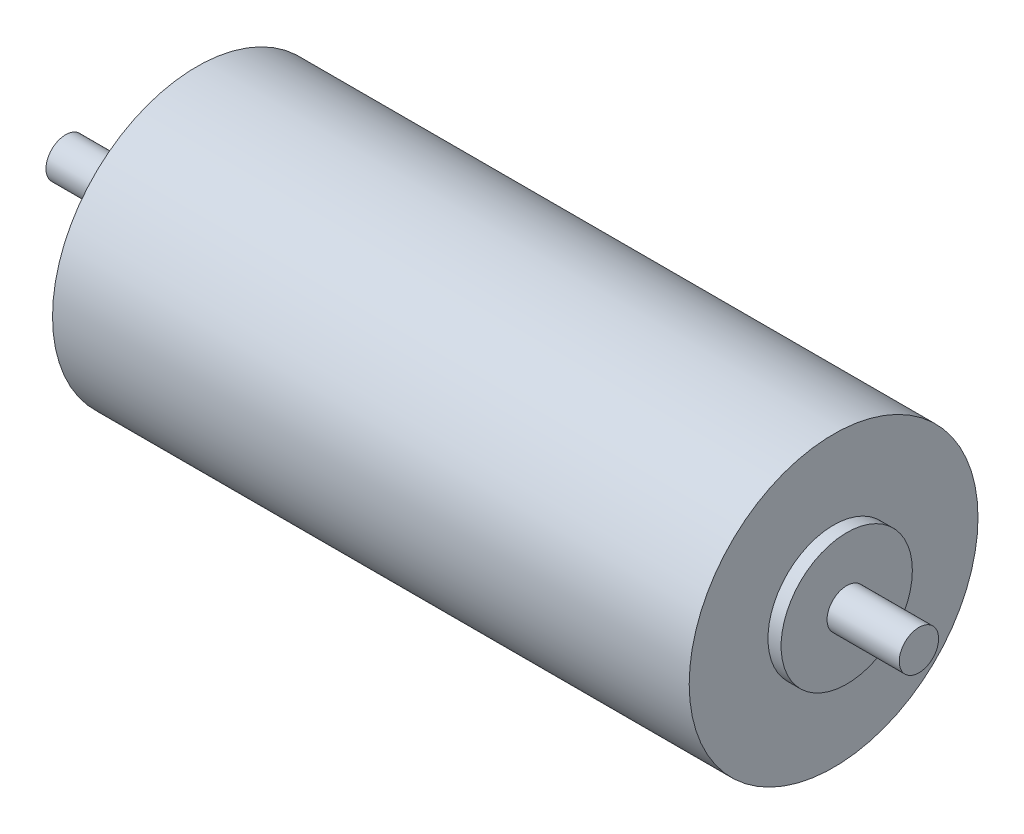
SolidWorks part; units mm, degrees
ref_plane "Vorne" through (0, 0, 0) normal (0, 0, 1) x (1, 0, 0)
ref_plane "Oben" through (0, 0, 0) normal (0, 1, 0) x (1, 0, 0)
ref_plane "Rechts" through (0, 0, 0) normal (1, 0, 0) x (0, 0, -1)
ref_plane "Ebene1" through (0, -15, 0) normal (0, 1, 0) x (1, 0, 0)
sketch "Skizze2" plane through (0, 0, 0) normal (0, 0, 1) x (1, 0, 0)
  line L0 (56.6731, 0) -> (-12.9638, 0) construction
  line L1 (-10, 0) -> (-10, 1.5)
  line L4 (-10, 1.5) -> (-1, 1.5)
  line L6 (-1, 1.5) -> (-1, 5)
  line L7 (-1, 5) -> (0, 5)
  line L8 (0, 5) -> (0, 11)
  line L9 (0, 11) -> (48.5, 11)
  line L10 (48.5, 11) -> (48.5, 5)
  line L12 (48.5, 5) -> (49.5, 5)
  line L13 (49.5, 5) -> (49.5, 1.5)
  line L15 (49.5, 1.5) -> (55, 1.5)
  line L16 (55, 1.5) -> (55, 0)
  line L18 (55, 0) -> (-10, 0)
  dimension "D1" = 22
  dimension "D2" = 3
  dimension "D3" = 10
  dimension "D4" = 3
  dimension "D5" = 10
  dimension "D6" = 10
  dimension "D7" = 9
  dimension "D8" = 5.5
  dimension "D9" = 6.5
  dimension "D10" = 48.5
revolve "Rotation1" add sketch "Skizze2" angle 360 about L0
